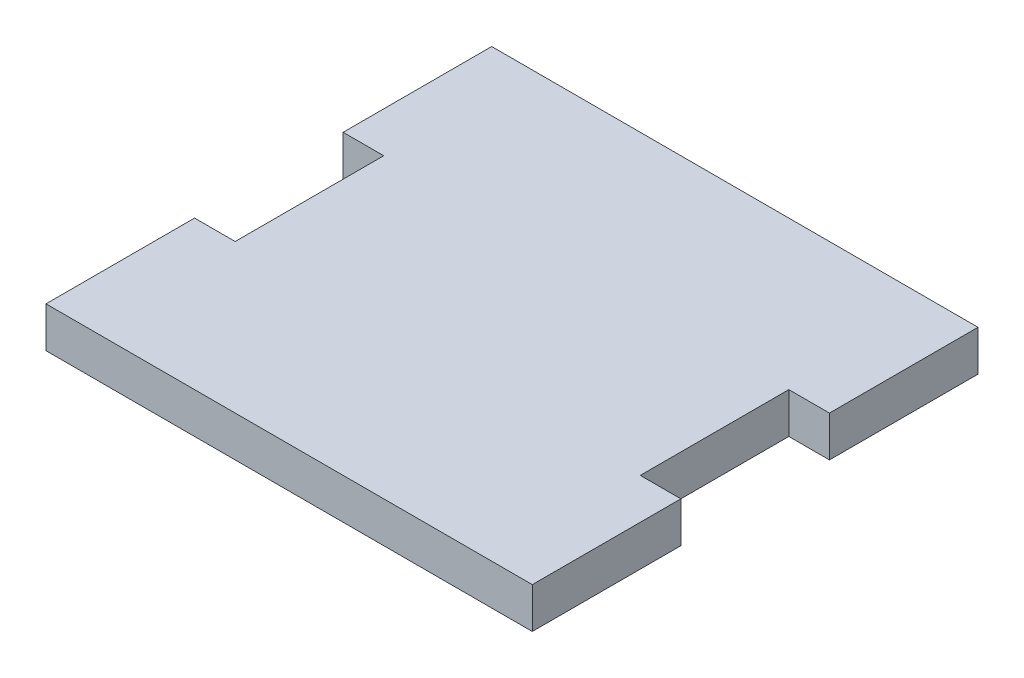
SolidWorks part; units mm, degrees
material "Corrugated Paper"
ref_plane "Front" through (0, 0, 0) normal (0, 0, 1) x (1, 0, 0)
ref_plane "Top" through (0, 0, 0) normal (0, 1, 0) x (1, 0, 0)
ref_plane "Right" through (0, 0, 0) normal (1, 0, 0) x (0, 0, -1)
sketch "Sketch1" plane through (0, 0, 0) normal (0, 1, 0) x (1, 0, 0)
  line L0 (4.1, 0) -> (0, 0)
  line L1 (0, 0) -> (49.1, 0) construction
  line L2 (0, 0) -> (0, 15)
  line L3 (0, 15) -> (49.1, 15)
  line L4 (49.1, 0) -> (49.1, 15)
  line L5 (45, 0) -> (49.1, 0)
  line L6 (4.1, 0) -> (4.1, -15)
  line L7 (4.1, -15) -> (45, -15) construction
  line L8 (45, 0) -> (45, -15)
  line L9 (4.1, -15) -> (45, -15) construction
  line L10 (0, -15) -> (4.1, -15)
  line L11 (0, -15) -> (0, -30)
  line L12 (0, -30) -> (49.1, -30)
  line L13 (49.1, -15) -> (49.1, -30)
  line L14 (45, -15) -> (49.1, -15)
  dimension "D1" = 15
  dimension "D2" = 49.1
  dimension "D3" = 15
  dimension "D4" = 4.1
  dimension "D5" = 15
extrude "Boss-Extrude1" add sketch "Sketch1" along normal blind 4.1
